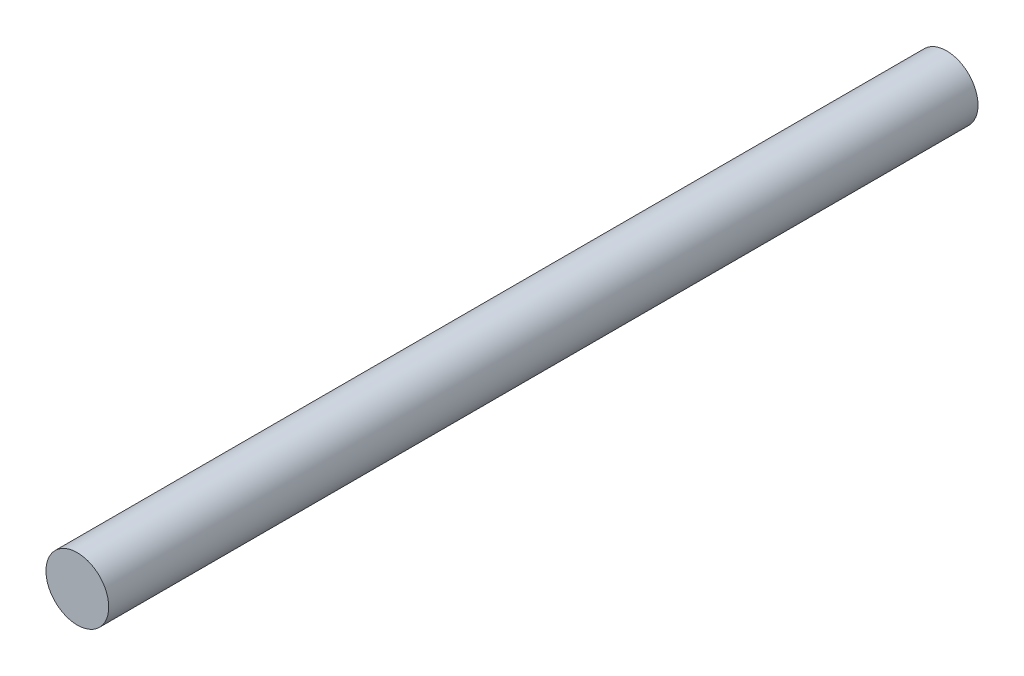
SolidWorks part; units mm, degrees
ref_plane "Front" through (0, 0, 0) normal (0, 0, 1) x (1, 0, 0)
ref_plane "Top" through (0, 0, 0) normal (0, 1, 0) x (1, 0, 0)
ref_plane "Right" through (0, 0, 0) normal (1, 0, 0) x (0, 0, -1)
sketch "草图1" plane through (0, 0, 0) normal (0, 0, 1) x (1, 0, 0)
  circle A0 centre (0, 0) radius 0.325
  dimension "D1" = 0.65
extrude "凸台-拉伸1" add sketch "草图1" along normal blind 9
